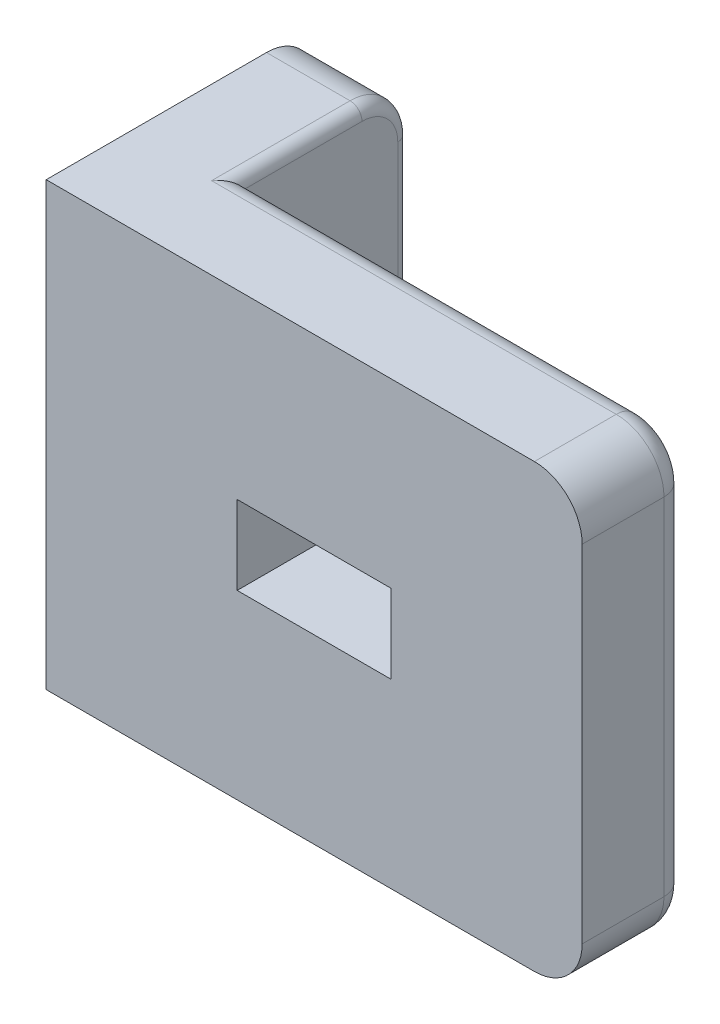
SolidWorks part; units mm, degrees
ref_plane "Front Plane" through (0, 0, 0) normal (0, 0, 1) x (1, 0, 0)
ref_plane "Top Plane" through (0, 0, 0) normal (0, 1, 0) x (1, 0, 0)
ref_plane "Right Plane" through (0, 0, 0) normal (1, 0, 0) x (0, 0, -1)
sketch "Sketch1" plane through (0, 0, 0) normal (0, 1, 0) x (1, 0, 0)
  line L0 (0, 0) -> (0, 11.2272) construction
  line L1 (0, 11.2272) -> (4, 11.2272) construction
  line L2 (4, 11.2272) -> (4, 4.4272) construction
  line L3 (4, 4.4272) -> (22.45, 4.4272) construction
  line L4 (22.45, 4.4272) -> (22.45, 0) construction
  line L5 (22.45, 0) -> (0, 0) construction
  line L6 (0, 0) -> (0, 11.2272)
  line L7 (0, 11.2272) -> (4, 11.2272)
  line L8 (4, 11.2272) -> (4, 4.4272)
  line L9 (4, 4.4272) -> (22.45, 4.4272)
  line L10 (22.45, 4.4272) -> (22.45, 0)
  line L11 (22.45, 0) -> (0, 0)
  dimension "D1" = 4
  dimension "D2" = 6.8
  dimension "D3" = 22.45
extrude "Boss-Extrude1" add sketch "Sketch1" along normal blind 18.5
sketch "Sketch2" plane through (0, 0, 0) normal (0, 0, 1) x (1, 0, 0)
  line L0 (0, 18.5) -> (22.45, 0) construction
  line L1 (22.45, 18.5) -> (0, 0) construction
  line L2 (0, 10.9) -> (22.45, 10.9) construction
  line L3 (0, 18.5) -> (0, 0) construction
  line L4 (22.45, 18.5) -> (22.45, 0) construction
  line L5 (0, 7.6) -> (22.45, 7.6) construction
  line L6 (14.45, 18.5) -> (14.45, 0) construction
  line L7 (0, 18.5) -> (22.45, 18.5) construction
  line L8 (0, 0) -> (22.45, 0) construction
  line L9 (8, 0) -> (8, 18.5) construction
  line L10 (14.45, 7.6) -> (8, 7.6)
  line L11 (8, 7.6) -> (8, 10.9)
  line L12 (8, 10.9) -> (14.45, 10.9)
  line L13 (14.45, 10.9) -> (14.45, 7.6)
  dimension "D1" = 7.6
  dimension "D2" = 7.6
  dimension "D3" = 8
  dimension "D4" = 8
extrude "Cut-Extrude1" cut sketch "Sketch2" against normal blind 4.5
sketch "Sketch3" plane through (4, 0, 0) normal (1, 0, 0) x (0, 0, -1)
  line L0 (4.4272, 0) -> (11.2272, 18.5) construction
  line L1 (11.2272, 0) -> (4.4272, 18.5) construction
  circle A0 centre (7.8272, 9.25) radius 2.15 construction
  circle A1 centre (7.8272, 9.25) radius 2.25
extrude "Cut-Extrude2" cut sketch "Sketch3" against normal blind 1.75
sketch "Sketch4" plane through (2.25, 0, 0) normal (1, 0, 0) x (0, 0, -1)
  circle A0 centre (7.8272, 9.25) radius 1.15 construction
  circle A2 centre (7.8272, 9.25) radius 2.25 construction
  circle A3 centre (7.8272, 9.25) radius 1.15
extrude "Cut-Extrude3" cut sketch "Sketch4" against normal blind 2.3
fillet "Fillet3" radius 2 1 edges at (2, 18.5, -11.2272)
fillet "Fillet4" radius 2 1 edges at (2, 0, -11.2272)
fillet "Fillet5" radius 2 1 edges at (22.45, 0, -2.2136)
fillet "Fillet6" radius 2 1 edges at (22.45, 18.5, -2.2136)
fillet "Fillet7" radius 1 4 edges at (14.45, 9.25, -4.4272) (11.225, 7.6, -4.4272) (8, 9.25, -4.4272) (11.225, 10.9, -4.4272)
fillet "Fillet8" radius 0.5 1 edges at (4, 9.25, -10.0772)
fillet "Fillet9" radius 1 1 edges at (2.25, 9.25, -10.0772)
fillet "Fillet10" radius 1 5 edges at (12.225, 18.5, -4.4272) (21.8642, 17.9142, -4.4272) (22.45, 9.25, -4.4272) (21.8642, 0.5858, -4.4272) (12.225, 0, -4.4272)
fillet "Fillet12" radius 0.5 5 edges at (4, 0, -6.3272) (4, 0.5858, -10.6415) (4, 9.25, -11.2272) (4, 17.9142, -10.6415) (4, 18.5, -6.3272)
